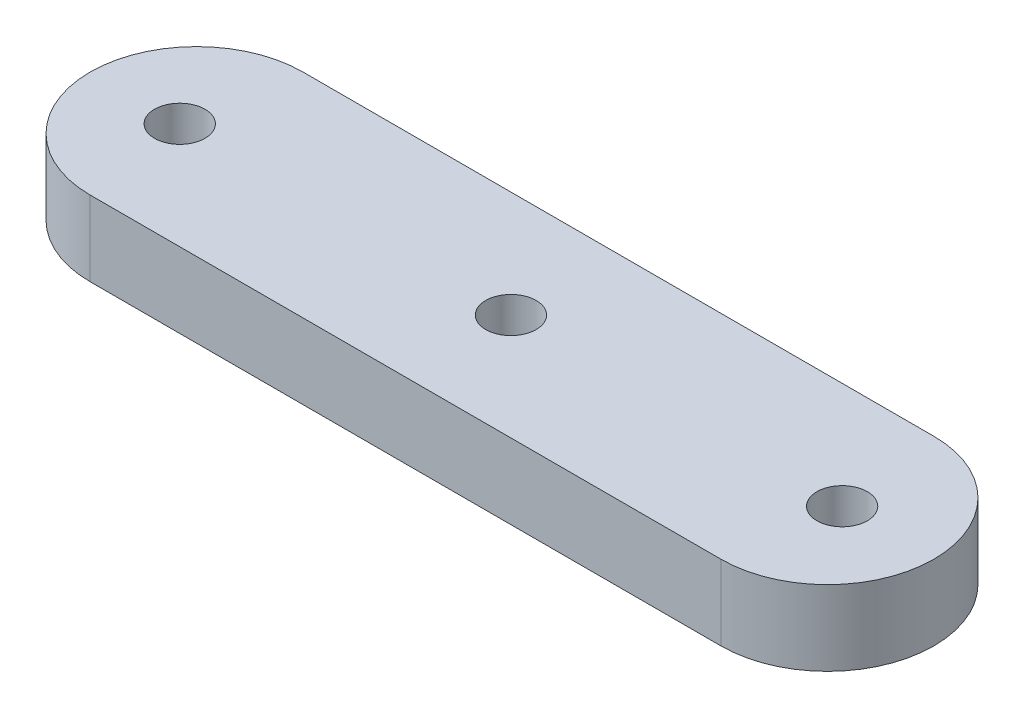
SolidWorks part; units mm, degrees
material "6061-T6 (SS)"
ref_plane "Front Plane" through (0, 0, 0) normal (0, 0, 1) x (1, 0, 0)
ref_plane "Top Plane" through (0, 0, 0) normal (0, 1, 0) x (1, 0, 0)
ref_plane "Right Plane" through (0, 0, 0) normal (1, 0, 0) x (0, 0, -1)
sketch "Sketch1" plane through (0, 0, 0) normal (0, 1, 0) x (1, 0, 0)
  line L6 (-19.9322, 0) -> (20.0678, 0) construction
  line L11 (-19.9322, 6.7509) -> (20.0678, 6.7509)
  line L12 (-19.9322, -6.7509) -> (20.0678, -6.7509)
  arc A3 (-19.9322, 6.7509) -> (-19.9322, -6.7509) centre (-19.9322, 0) ccw
  arc A4 (20.0678, -6.7509) -> (20.0678, 6.7509) centre (20.0678, 0) ccw
  point P0 (-26.6832, 0)
  point P1 (26.8187, 0)
  point P12 (0, 0)
  point P13 (21, 0)
  point P14 (-21, 0)
  point P24 (-31.4439, 0)
  point P25 (31.5795, 0)
  point P28 (0.0678, 0)
  dimension "D1" = 53.5019
  dimension "D2" = 13.5019
extrude "Boss-Extrude1" add sketch "Sketch1" along normal blind 4.763
hole_wizard "M3 Clearance Hole1" positions "Sketch3" profile "Sketch2" hole size "M3" standard "ANSI Metric" end condition up to next
sketch "Sketch3" plane through (0, 4.763, 0) normal (0, 1, 0) x (1, 0, 0)
  line L0 (-19.9322, 6.7509) -> (-19.9322, -6.7509) construction
  line L2 (20.0678, 6.7509) -> (20.0678, -6.7509) construction
  line L4 (-19.9322, 0) -> (20.0678, 0) construction
  point P0 (-21, 0)
  point P2 (0, 0)
  point P5 (21, 0)
  dimension "D1" = 21
  dimension "D2" = 21
sketch "Sketch2" plane through (-21, 4.763, 0) normal (1, 0, 0) x (0, 0, 1)
  line L0 (0, 0) -> (0, 4.763)
  line L1 (0, 4.763) -> (1.6, 4.763)
  line L2 (1.6, 4.763) -> (1.6, 0)
  line L5 (1.6, 0) -> (0, 0)
  line L11 (0, -6.35) -> (0, 107.95) construction
  dimension "Thru Hole Dia." = 3.2
  dimension "Thru Hole Depth" = 4.763
